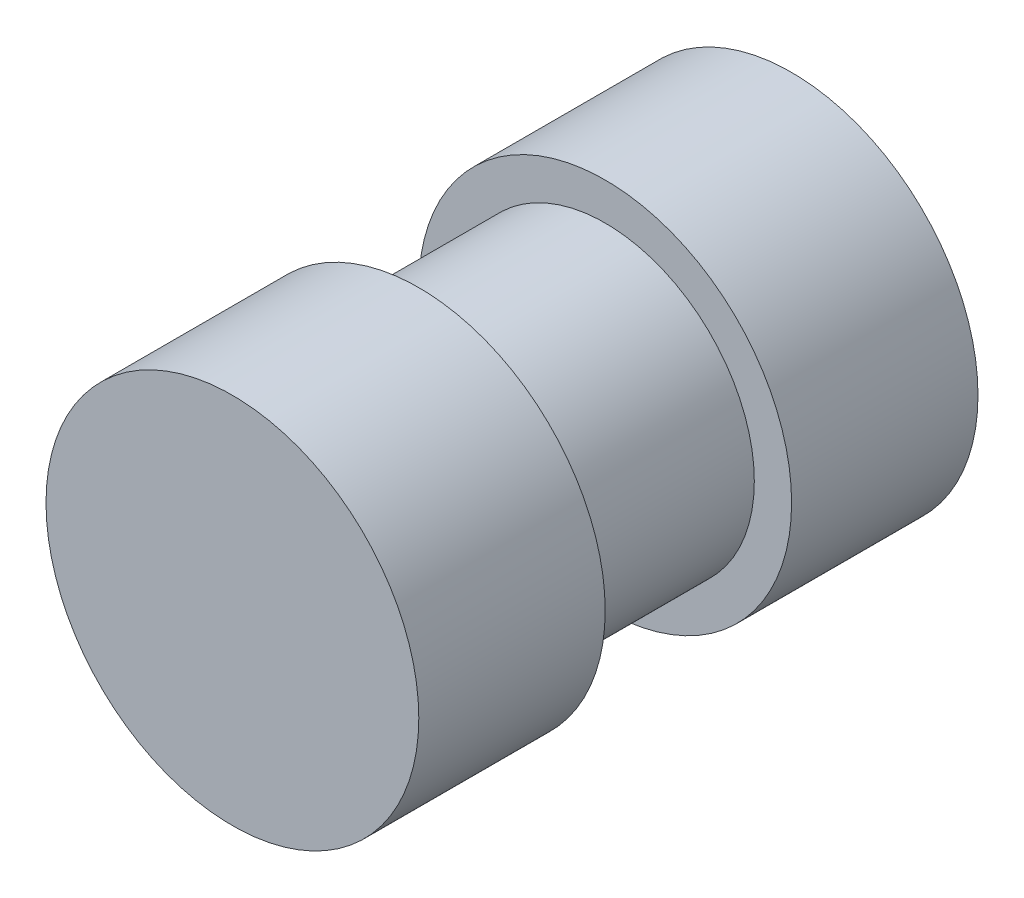
SolidWorks part; units mm, degrees
ref_plane "前基準面" through (0, 0, 0) normal (0, 0, 1) x (1, 0, 0)
ref_plane "上基準面" through (0, 0, 0) normal (0, 1, 0) x (1, 0, 0)
ref_plane "右基準面" through (0, 0, 0) normal (1, 0, 0) x (0, 0, -1)
sketch "草圖1" plane through (0, 0, 0) normal (0, 0, 1) x (1, 0, 0)
  circle A0 centre (0, 0) radius 4
  dimension "D1" = 8
extrude "填料-伸長1" add sketch "草圖1" along normal mid plane 15
sketch "草圖3" plane through (0, 0, 7.5) normal (0, 0, 1) x (1, 0, 0)
  circle A0 centre (0, 0) radius 5
  dimension "D1" = 10
extrude "填料-伸長2" add sketch "草圖3" against normal blind 5
mirror "鏡射1" about plane through (0, 0, 0) normal (0, 0, 1) of "填料-伸長2"
